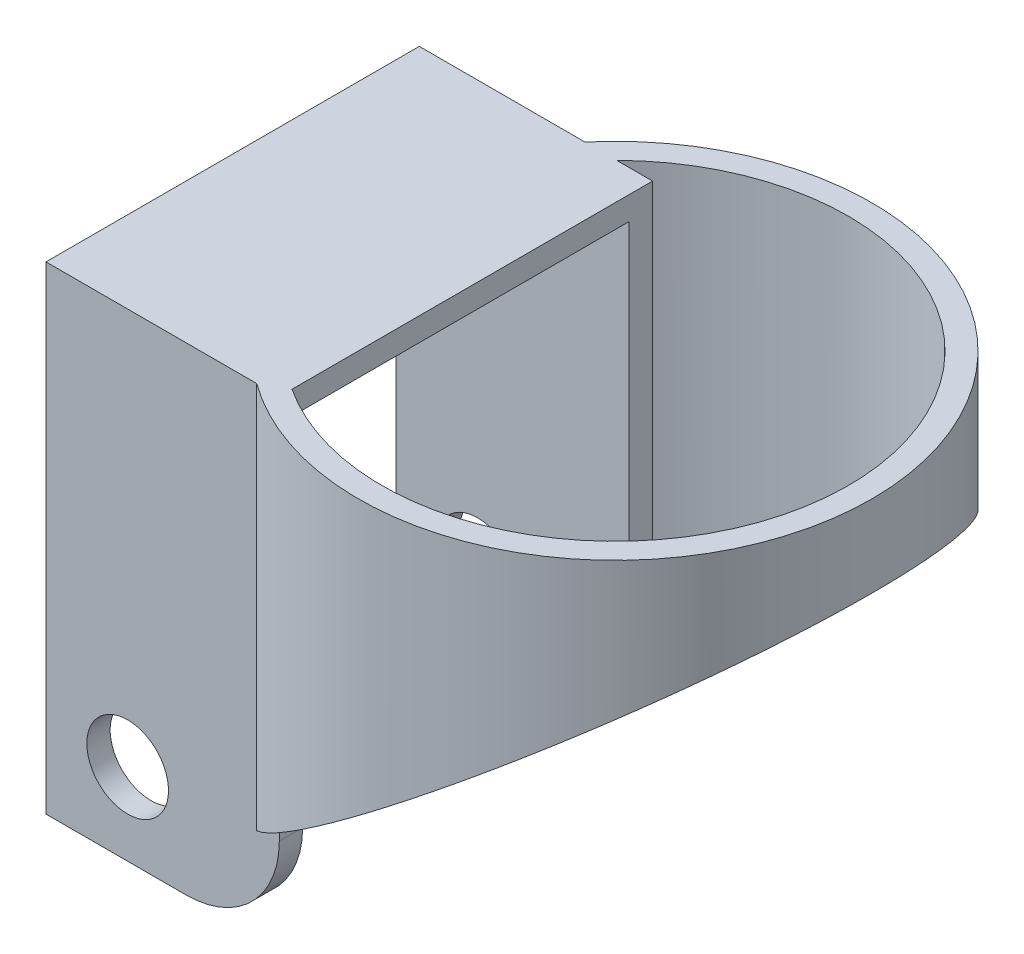
SolidWorks part; units mm, degrees
material "1023 Carbon Steel Sheet (SS)"
ref_plane "Front Plane" through (0, 0, 0) normal (0, 0, 1) x (1, 0, 0)
ref_plane "Top Plane" through (0, 0, 0) normal (0, 1, 0) x (1, 0, 0)
ref_plane "Right Plane" through (0, 0, 0) normal (1, 0, 0) x (0, 0, -1)
sketch "Sketch1" plane through (0, 0, 0) normal (0, 1, 0) x (1, 0, 0)
  circle A0 centre (0, 0) radius 22
  circle A1 centre (0, 0) radius 20
  dimension "D1" = 44
  dimension "D2" = 40
extrude "Boss-Extrude1" add sketch "Sketch1" along normal blind 40
sketch "Sketch2" plane through (0, 0, 0) normal (0, 0, 1) x (1, 0, 0)
  line L0 (22, 33) -> (-22, 0)
  line L1 (22, 0) -> (22, 40) construction
  line L2 (-22, 0) -> (22, 0) construction
  line L3 (-22, 0) -> (22, 0)
  line L4 (22, 0) -> (22, 33)
  dimension "D1" = 7
extrude "Cut-Extrude1" cut sketch "Sketch2" against normal through all both and the other way through all
ref_plane "Plane1" through (-31, 0, 0) normal (1, 0, 0) x (0, 0, -1)
sketch "Sketch3" plane through (-31, 0, 0) normal (1, 0, 0) x (0, 0, -1)
  line L0 (14.208, 40) -> (-17.792, 40)
  line L1 (12.208, 38) -> (12.208, 1)
  line L2 (-17.792, 40) -> (-17.792, -1)
  line L3 (-17.792, -1) -> (-15.792, -1)
  line L4 (14.208, 40) -> (14.208, -1)
  line L5 (-10.9518, 40) -> (14.208, -1) construction
  line L6 (-17.792, -1) -> (4.0938, 40) construction
  line L7 (22, 40) -> (-22, 40) construction
  line L9 (-15.792, 38) -> (-15.792, 1)
  line L10 (12.208, 38) -> (-15.792, 38)
  line L11 (-15.792, 1) -> (-15.792, -1)
  line L12 (12.208, 1) -> (12.208, -1)
  line L13 (12.208, -1) -> (14.208, -1)
  line L14 (-17.792, -1) -> (14.208, -1) construction
  line L15 (-15.792, 1) -> (12.208, 1) construction
  point P0 (-2.9055, 26.8878)
  dimension "D1" = 32
  dimension "D2" = 41
  dimension "D3" = 2
extrude "Boss-Extrude2" add sketch "Sketch3" along normal blind 20
sketch "Sketch4" plane through (0, 0, 0) normal (1, 0, 0) x (0, 0, -1)
  line L0 (-15.792, -1) -> (12.208, -1)
  line L8 (12.208, -1) -> (14.208, -1)
  line L9 (12.208, 38) -> (12.208, -1)
  line L10 (-15.792, 38) -> (12.208, 38)
  line L11 (-15.792, -1) -> (-15.792, 38)
  line L12 (-17.792, -1) -> (-15.792, -1)
  line L13 (-17.792, 40) -> (-17.792, -1)
  line L14 (14.208, 40) -> (-17.792, 40)
  line L15 (14.208, -1) -> (14.208, 40)
  line L17 (12.208, 38) -> (12.208, -1)
  line L18 (-15.792, 38) -> (12.208, 38)
  line L19 (-15.792, -1) -> (-15.792, 38)
  dimension "D1" = 0
extrude "Cut-Extrude2" cut sketch "Sketch4" against normal through all
sketch "Sketch5" plane through (0, 0, -14.208) normal (0, 0, -1) x (-1, 0, 0)
  line L0 (11, -1) -> (31, -1) construction
  line L1 (31, 22.55) -> (31, -22.55) construction
  circle A0 centre (24, 6) radius 3.5
  dimension "D1" = 7
  dimension "D2" = 7
  dimension "D3" = 7
extrude "Cut-Extrude3" cut sketch "Sketch5" against normal through all both and the other way through all
fillet "Fillet1" radius 8 2 edges at (-11, -1, 16.792) (-11, -1, -13.208)
